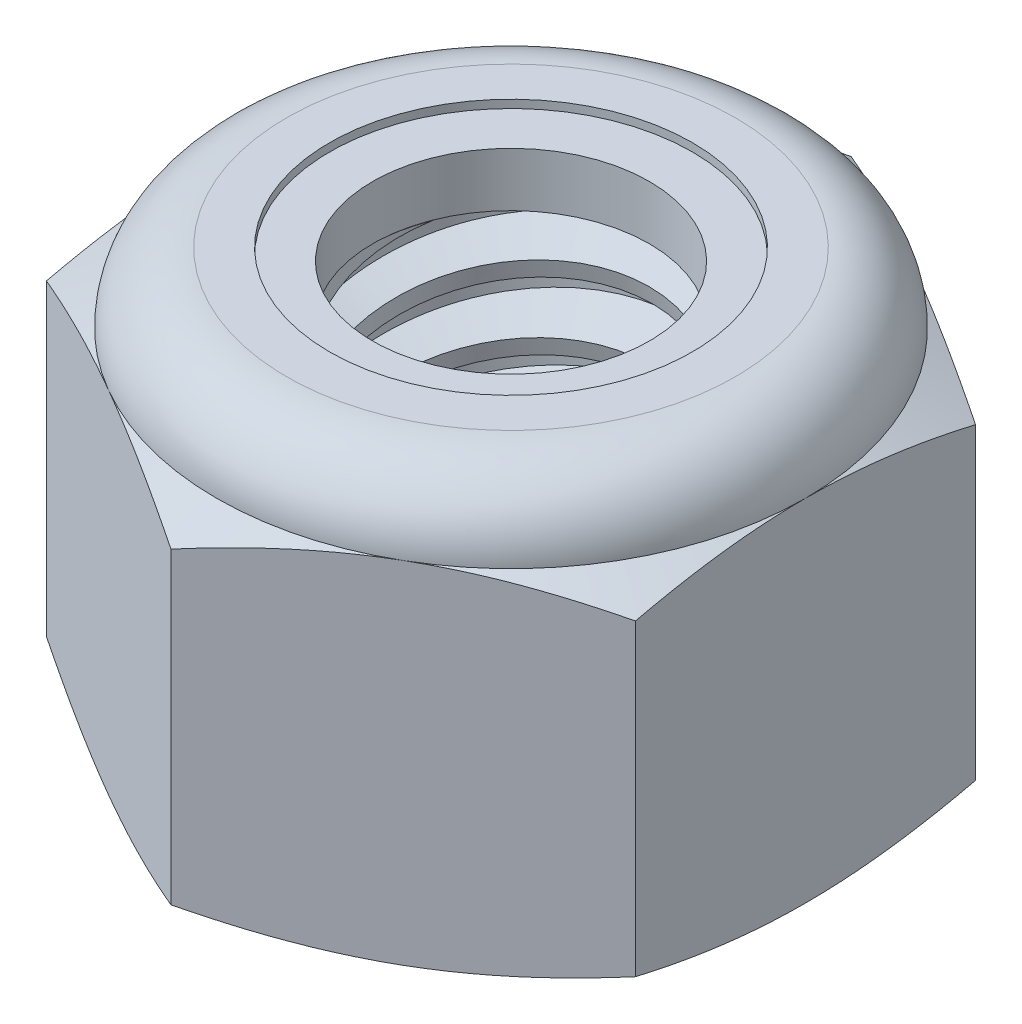
SolidWorks part; units mm, degrees
material "Stainless Steel (ferritic)"
ref_plane "Front" through (0, 0, 0) normal (0, 0, 1) x (1, 0, 0)
ref_plane "Top" through (0, 0, 0) normal (0, 1, 0) x (1, 0, 0)
ref_plane "Right" through (0, 0, 0) normal (1, 0, 0) x (0, 0, -1)
sketch "Sketch1" plane through (0, 0, 0) normal (0, 1, 0) x (1, 0, 0)
  line L1 (0, 6.4158) -> (-5.5563, 3.2079)
  line L2 (-5.5563, 3.2079) -> (-5.5563, -3.2079)
  line L3 (-5.5563, -3.2079) -> (0, -6.4158)
  line L4 (0, -6.4158) -> (5.5562, -3.2079)
  line L5 (5.5562, -3.2079) -> (5.5562, 3.2079)
  line L6 (5.5562, 3.2079) -> (0, 6.4158)
  circle A0 centre (0, 0) radius 5.5563 construction
  dimension "Hex Flats" = 11.1125
extrude "Extrude1" add sketch "Sketch1" along normal blind 7.9375
sketch "Sketch2" plane through (0, 0, 0) normal (1, 0, 0) x (0, 0, -1)
  line L0 (-3.175, 0) -> (-3.175, 7.9375) construction
  line L1 (0, 0) -> (3.175, 0)
  line L2 (0, 0) -> (0, 7.9375)
  line L3 (0, 7.9375) -> (3.175, 7.9375)
  line L4 (3.175, 0) -> (3.175, 7.9375)
  line L5 (-3.2079, 7.9375) -> (3.2079, 7.9375) construction
  line L7 (0, -3.175) -> (0, 0) construction
  dimension "Thread Dia" = 6.35
revolve "Revolve1" add sketch "Sketch2" angle 360 about L7
sketch "Sketch3" plane through (0, 0, 0) normal (1, 0, 0) x (0, 0, -1)
  line L0 (3.175, 7.9375) -> (-3.175, 7.9375) construction
  line L1 (-3.175, 7.9375) -> (-3.175, 6.6675) construction
  line L2 (-3.175, 6.6675) -> (3.175, 7.9375) construction
  line L3 (3.175, 7.9375) -> (3.2061, 7.7818) construction
  line L4 (3.2061, 7.7818) -> (3.4241, 6.6922)
  line L5 (3.4241, 6.6922) -> (2.6722, 6.9465)
  line L6 (2.6722, 6.9465) -> (2.6099, 7.2579)
  line L7 (2.6099, 7.2579) -> (3.2061, 7.7818)
  line L8 (2.641, 7.1022) -> (3.3151, 7.237) construction
  line L9 (3.175, 7.9375) -> (3.175, 7.209) construction
  line L10 (3.175, 7.209) -> (-3.175, 5.939) construction
  line L11 (-3.175, 5.939) -> (-3.175, 6.6675) construction
  line L12 (-0.2727, 7.9375) -> (0.2727, 5.2105) construction
  line L13 (-3.175, 0) -> (-3.175, 7.9375) construction
  line L14 (0, 7.9375) -> (3.175, 7.9375) construction
  line L15 (3.175, 0) -> (3.175, 7.9375) construction
  point P13 (0, 6.574)
  dimension "D1" = 0.1588
  dimension "D2" = 0.3175
  dimension "Thread Pitch" = 1.27
  dimension "D4" = 60
  dimension "D5" = 1.27
revolve "Cut-Revolve1" cut sketch "Sketch3" angle 360 about L12
pattern_linear "LPattern1" count 6 spacing 1.27 along (0, -1, 0) count 2 spacing 1.27 along (0, 1, 0) of "Cut-Revolve1"
sketch "Sketch4" plane through (0, 0, 0) normal (1, 0, 0) x (0, 0, -1)
  line L0 (0, 7.9375) -> (3.175, 7.9375)
  line L1 (3.175, 7.9375) -> (2.6099, 7.674)
  line L2 (2.6099, 7.674) -> (2.6099, 0.2635)
  line L3 (2.6099, 0.2635) -> (3.175, 0)
  line L4 (3.175, 0) -> (0, 0)
  line L5 (0, 0) -> (0, 7.9375)
  line L6 (3.175, 0) -> (3.175, 7.9375) construction
  line L7 (0, 7.9375) -> (3.175, 7.9375) construction
  line L8 (0, 0) -> (3.175, 0) construction
  line L9 (0, 0) -> (0, 7.9375) construction
  line L10 (0, 7.9375) -> (0, 8.561) construction
  dimension "D1" = 25
revolve "Cut-Revolve2" cut sketch "Sketch4" angle 360 about L10
combine bodies "Combine1" operation type subtract main body 112 bodies to subtract 111
sketch "Sketch5" plane through (0, 0, 0) normal (1, 0, 0) x (0, 0, -1)
  line L0 (0, 0) -> (5.5563, 0)
  line L1 (5.5563, 0) -> (6.4158, 0.4008)
  line L2 (6.4158, 0.4008) -> (6.4158, 6.2138)
  line L3 (6.4158, 6.2138) -> (5.5563, 6.6146)
  line L4 (4.2333, 7.9375) -> (4.2333, 9.2075)
  line L5 (4.2333, 9.2075) -> (7.6858, 9.2075)
  line L6 (7.6858, 9.2075) -> (7.6858, -1.27)
  line L7 (7.6858, -1.27) -> (0, -1.27)
  line L8 (0, -1.27) -> (0, 0)
  line L9 (5.5563, 6.6146) -> (5.5563, 0) construction
  line L10 (0, 0) -> (3.175, 0) construction
  line L13 (6.4158, 3.3073) -> (7.6858, 3.3073) construction
  line L14 (6.4158, 7.9375) -> (6.4158, 0) construction
  line L15 (0, 0) -> (0, 9.2075) construction
  line L20 (0, 9.2075) -> (4.2333, 9.2075) construction
  line L22 (0, 7.9375) -> (3.175, 7.9375) construction
  arc A0 (5.5563, 6.6146) -> (4.2333, 7.9375) centre (4.2333, 6.6146) ccw
  dimension "D1" = 25
  dimension "D2" = 1.27
  dimension "D3" = 7.9375
  dimension "D4" = 1.3229
revolve "Cut-Revolve3" cut sketch "Sketch5" angle 360 about L15
sketch "Sketch6" plane through (0, 0, 0) normal (1, 0, 0) x (0, 0, -1)
  line L0 (0, 6.6146) -> (5.4039, 6.6146)
  line L1 (4.2333, 7.7851) -> (3.4216, 7.7851)
  line L2 (0, 9.2075) -> (0, 6.6146)
  line L3 (3.4216, 9.2075) -> (0, 9.2075)
  line L4 (0, 9.2075) -> (4.2333, 9.2075) construction
  line L5 (0, 0) -> (0, 9.2075) construction
  line L6 (0, 9.2075) -> (0, 44.323) construction
  line L7 (3.4216, 7.7851) -> (3.4216, 9.2075)
  line L8 (4.2333, 7.9375) -> (4.2333, 7.7851) construction
  line L9 (3.4216, 7.7851) -> (2.6099, 7.7851) construction
  line L10 (2.6099, 7.7851) -> (2.6099, 7.674) construction
  arc A0 (5.4039, 6.6146) -> (4.2333, 7.7851) centre (4.2333, 6.6146) ccw
  arc A1 (5.5563, 6.6146) -> (4.2333, 7.9375) centre (4.2333, 6.6146) ccw construction
  dimension "D1" = 0.1524
revolve "Cut-Revolve4" cut sketch "Sketch6" angle 360 about L6
sketch "Sketch7" plane through (0, 0, 0) normal (1, 0, 0) x (0, 0, -1)
  line L0 (2.6099, 6.6908) -> (5.325, 6.6908)
  line L1 (4.2333, 7.7089) -> (2.6099, 7.7089)
  line L2 (2.6099, 7.7089) -> (2.6099, 6.6908)
  line L3 (2.6099, 6.6908) -> (0, 6.6908) construction
  line L4 (0, 6.6908) -> (0, 7.7089) construction
  line L5 (0, 7.7089) -> (2.6099, 7.7089) construction
  line L6 (2.6099, 6.6908) -> (2.6099, 6.6146) construction
  line L7 (0, 6.6146) -> (5.4039, 6.6146) construction
  line L8 (4.2333, 7.7089) -> (4.2333, 7.7851) construction
  arc A0 (5.325, 6.6908) -> (4.2333, 7.7089) centre (4.2333, 6.6146) ccw
  arc A2 (5.4039, 6.6146) -> (4.2333, 7.7851) centre (4.2333, 6.6146) ccw construction
  dimension "D1" = 0.0762
revolve "Revolve2" add sketch "Sketch7" angle 360 about L4
equation "\"D1@Sketch3\"=\"Thread Pitch@Sketch3\"/8"
equation "\"D2@Sketch3\"=\"Thread Pitch@Sketch3\"/4"
equation "\"D5@Sketch3\"=\"Thread Pitch@Sketch3\""
equation "\"D4@LPattern1\"=\"Thread Pitch@Sketch3\""
equation "\"D3@LPattern1\"=\"Thread Pitch@Sketch3\""
equation "\"D1@LPattern1\"=\"Height@Extrude1\"/\"Thread Pitch@Sketch3\""
equation "\"D4@Sketch5\"=\"Height@Extrude1\"/6"
